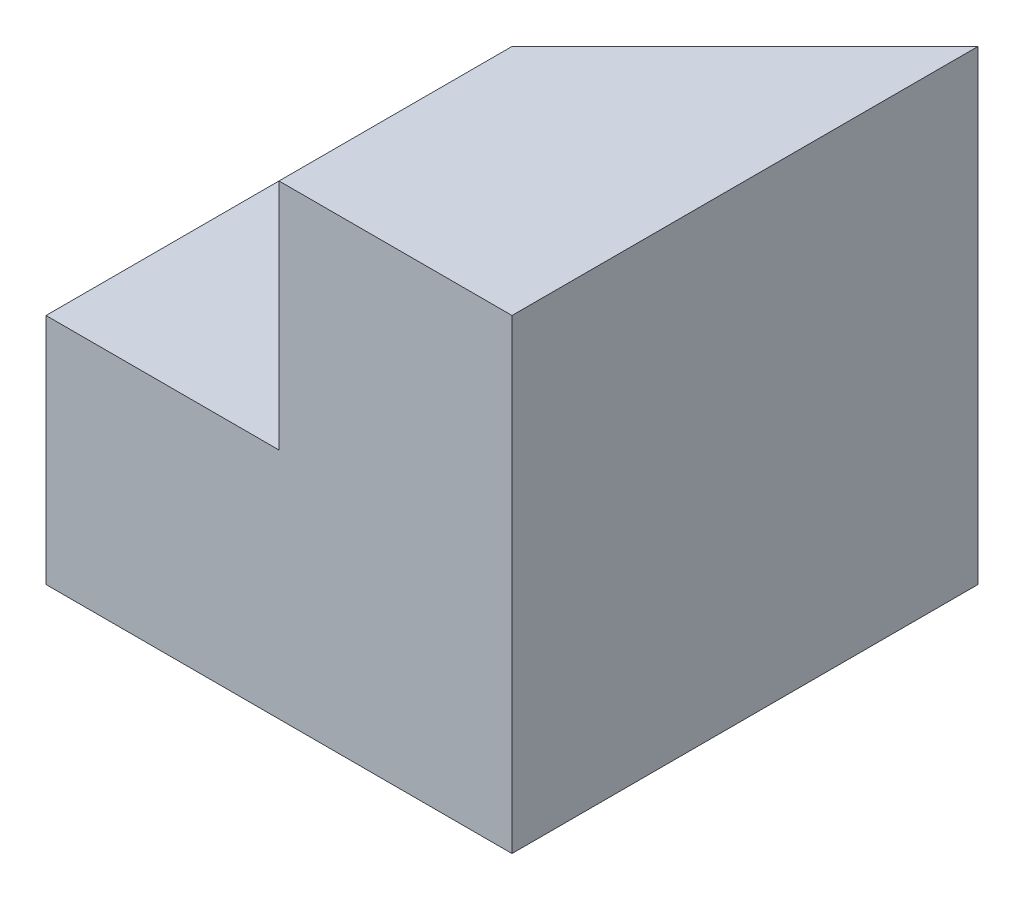
SolidWorks part; units mm, degrees
ref_plane "Front Plane" through (0, 0, 0) normal (0, 0, 1) x (1, 0, 0)
ref_plane "Top Plane" through (0, 0, 0) normal (0, 1, 0) x (1, 0, 0)
ref_plane "Right Plane" through (0, 0, 0) normal (1, 0, 0) x (0, 0, -1)
sketch "Sketch1" plane through (0, 0, 0) normal (0, 0, 1) x (1, 0, 0)
  line L1 (0, 0) -> (40, 0)
  line L2 (0, 0) -> (0, 40)
  line L3 (0, 40) -> (40, 40)
  line L4 (40, 0) -> (40, 40)
  dimension "D1" = 40
  dimension "D2" = 40
extrude "Boss-Extrude1" add sketch "Sketch1" along normal blind 40
sketch "Sketch2" plane through (0, 0, 40) normal (0, 0, 1) x (1, 0, 0)
  line L1 (0, 40) -> (20, 40)
  line L2 (0, 40) -> (0, 20)
  line L3 (0, 20) -> (20, 20)
  line L4 (20, 40) -> (20, 20)
  dimension "D1" = 20
  dimension "D2" = 20
extrude "Cut-Extrude1" cut sketch "Sketch2" against normal blind 40
sketch "Sketch3" plane through (0, 40, 0) normal (0, 1, 0) x (1, 0, 0)
  line L0 (40, 0) -> (20, -20)
  line L1 (20, 0) -> (20, -40) construction
  line L2 (20, -20) -> (20, 0)
  line L3 (20, 0) -> (40, 0)
extrude "Cut-Extrude2" cut sketch "Sketch3" against normal blind 20
